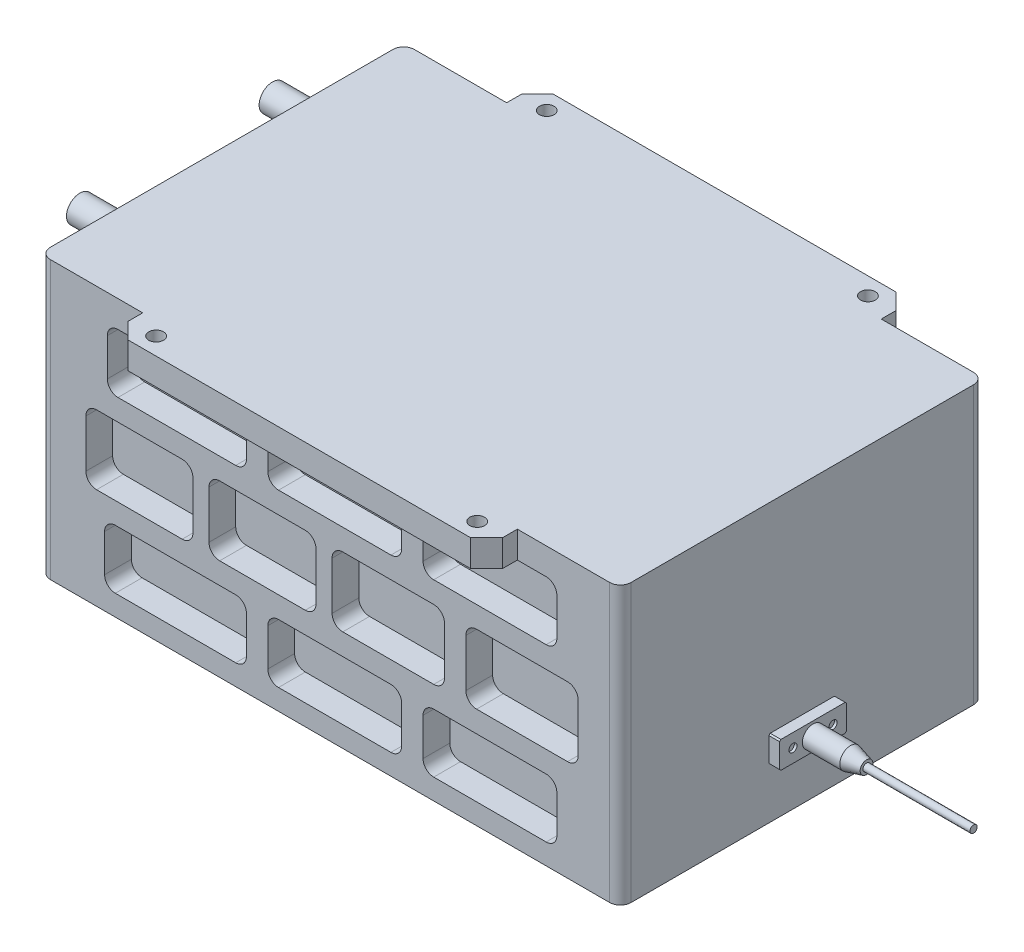
SolidWorks part; units mm, degrees
ref_plane "Front Plane" through (0, 0, 0) normal (0, 0, 1) x (1, 0, 0)
ref_plane "Top Plane" through (0, 0, 0) normal (0, 1, 0) x (1, 0, 0)
ref_plane "Right Plane" through (0, 0, 0) normal (1, 0, 0) x (0, 0, -1)
sketch "Sketch1" plane through (0, 0, 0) normal (0, 1, 0) x (1, 0, 0)
  line L1 (0, 0) -> (-217, 0)
  line L2 (0, 0) -> (0, 136)
  line L3 (0, 136) -> (-217, 136)
  line L4 (-217, 0) -> (-217, 136)
  dimension "D1" = 136
  dimension "D2" = 217
extrude "Boss-Extrude1" add sketch "Sketch1" along normal blind 103.6
sketch "Sketch2" plane through (0, 103.6, 0) normal (0, 1, 0) x (1, 0, 0)
  line L0 (-217, 0) -> (0, 0) construction
  line L1 (-178.5, 147.5) -> (-38.5, 147.5)
  line L2 (-178.5, 147.5) -> (-178.5, -11.5)
  line L3 (-178.5, -11.5) -> (-38.5, -11.5)
  line L4 (-38.5, 147.5) -> (-38.5, -11.5)
  line L5 (-217, 136) -> (-217, 0) construction
  dimension "D1" = 159
  dimension "D2" = 11.5
  dimension "D3" = 140
  dimension "D4" = 38.5
extrude "Boss-Extrude2" add sketch "Sketch2" against normal blind 10
sketch "Sketch3" plane through (0, 103.6, 0) normal (0, 1, 0) x (1, 0, 0)
  circle A0 centre (-168.5, 141) radius 2.75
  circle A1 centre (-48.5, 141) radius 2.75
  circle A2 centre (-168.5, -5) radius 2.75
  circle A3 centre (-48.5, -5) radius 2.75
  dimension "D5" = 5.5
  dimension "D6" = 5.5
  dimension "D7" = 5.5
  dimension "D8" = 5.5
  dimension "D1" = 120
  dimension "D3" = 146
extrude "Cut-Extrude1" cut sketch "Sketch3" against normal blind 10
sketch "Sketch5" plane through (0, 0, 0) normal (1, 0, 0) x (0, 0, -1)
  line L2 (55.5, 28.8) -> (80.5, 28.8)
  line L3 (55.5, 28.8) -> (55.5, 18.8)
  line L4 (55.5, 18.8) -> (80.5, 18.8)
  line L5 (80.5, 28.8) -> (80.5, 18.8)
  dimension "D3" = 25
  dimension "D5" = 10
extrude "Boss-Extrude3" add sketch "Sketch5" along normal blind 4
sketch "Sketch6" plane through (4, 0, 0) normal (1, 0, 0) x (0, 0, -1)
  line L1 (0, 103.6) -> (136, 103.6) construction
  circle A0 centre (68, 23.8) radius 4
  dimension "D1" = 8
  dimension "D2" = 79.8
extrude "Boss-Extrude4" add sketch "Sketch6" along normal blind 20
chamfer "Chamfer1" distance 6 angle 15 1 edges at (24, 23.8, -72)
sketch "Sketch7" plane through (-217, 0, 0) normal (-1, 0, 0) x (0, 0, 1)
  line L0 (-136, 103.6) -> (0, 103.6) construction
  circle A0 centre (-104, 93.6) radius 7.5
  circle A1 centre (-32, 93.6) radius 7.5
  point P6 (-68, 103.6)
  dimension "D1" = 72
  dimension "D2" = 36
  dimension "D3" = 15
  dimension "D4" = 15
  dimension "D5" = 10
extrude "Boss-Extrude5" add sketch "Sketch7" along normal blind 2
sketch "Sketch8" plane through (4, 0, 0) normal (1, 0, 0) x (0, 0, -1)
  circle A0 centre (75.5, 23.8) radius 1.5
  circle A1 centre (60.5, 23.8) radius 1.5
  circle A2 centre (68, 23.8) radius 2.3923 construction
  dimension "D1" = 15
  dimension "D2" = 7.5
  dimension "D3" = 3
  dimension "D4" = 3
extrude "Cut-Extrude2" cut sketch "Sketch8" against normal blind 1
chamfer "Chamfer2" distance 0.5 angle 45 4 edges at (2, 28.8, -55.5) (2, 28.8, -80.5) (2, 18.8, -55.5) (2, 18.8, -80.5)
chamfer "Chamfer3" distance 6 angle 45 4 edges at (-178.5, 98.6, -147.5) (-38.5, 98.6, -147.5) (-178.5, 98.6, 11.5) (-38.5, 98.6, 11.5)
sketch "Sketch9" plane through (-219, 0, 0) normal (-1, 0, 0) x (0, 0, 1)
  circle A0 centre (-104, 93.6) radius 5
  circle A1 centre (-32, 93.6) radius 5
  circle A2 centre (-104, 93.6) radius 4
  circle A3 centre (-32, 93.6) radius 4
  dimension "D1" = 10
  dimension "D2" = 10
  dimension "D3" = 8
  dimension "D4" = 8
extrude "Boss-Extrude6" add sketch "Sketch9" along normal blind 15
fillet "Fillet2" radius 4 4 edges at (-217, 51.8, 0) (-217, 51.8, -136) (0, 51.8, 0) (0, 51.8, -136)
sketch "Sketch11" plane through (0, 0, -136) normal (0, 0, -1) x (-1, 0, 0)
  line L0 (38.5, 93.6) -> (73.7445, 93.6)
  line L1 (178.5, 93.6) -> (191.7445, 93.6)
  line L2 (159.7445, 37.7329) -> (199.7445, 37.7329)
  line L4 (192.7445, 7.7329) -> (139.7445, 7.7329)
  line L5 (113.7445, 37.7329) -> (153.7445, 37.7329)
  line L7 (23.7445, 93.6) -> (38.5, 93.6)
  line L8 (23.7445, 71.6) -> (73.7445, 71.6)
  line L9 (15.7445, 63.6) -> (57.7445, 63.6)
  line L10 (15.7445, 37.7329) -> (57.7445, 37.7329)
  line L11 (23.7445, 29.7329) -> (73.7445, 29.7329)
  line L12 (23.7445, 93.6) -> (23.7445, 71.6)
  line L13 (73.7445, 93.6) -> (73.7445, 71.6)
  line L14 (81.7445, 93.6) -> (81.7445, 71.6)
  line L15 (131.7445, 93.6) -> (131.7445, 71.6)
  line L16 (139.7445, 93.6) -> (139.7445, 71.6)
  line L17 (191.7445, 93.6) -> (191.7445, 71.6)
  line L18 (57.7445, 63.6) -> (57.7445, 37.7329)
  line L19 (65.7445, 63.6) -> (65.7445, 37.7329)
  line L20 (81.7445, 71.6) -> (131.7445, 71.6)
  line L21 (81.7445, 93.6) -> (131.7445, 93.6)
  line L22 (139.7445, 93.6) -> (178.5, 93.6)
  line L23 (139.7445, 71.6) -> (191.7445, 71.6)
  line L24 (107.7445, 63.6) -> (107.7445, 37.7329)
  line L25 (113.7445, 63.6) -> (113.7445, 37.7329)
  line L26 (153.7445, 63.6) -> (153.7445, 37.7329)
  line L27 (159.7445, 63.6) -> (159.7445, 37.7329)
  line L28 (73.7445, 7.7329) -> (23.7445, 7.7329)
  line L29 (131.7445, 7.7329) -> (81.7445, 7.7329)
  line L30 (192.7445, 29.7329) -> (192.7445, 7.7329)
  line L31 (139.7445, 29.7329) -> (139.7445, 7.7329)
  line L32 (131.7445, 29.7329) -> (131.7445, 7.7329)
  line L33 (81.7445, 29.7329) -> (81.7445, 7.7329)
  line L34 (73.7445, 29.7329) -> (73.7445, 7.7329)
  line L35 (23.7445, 29.7329) -> (23.7445, 7.7329)
  line L36 (81.7445, 29.7329) -> (131.7445, 29.7329)
  line L37 (139.7445, 29.7329) -> (192.7445, 29.7329)
  line L38 (15.7445, 63.6) -> (15.7445, 37.7329)
  line L39 (199.7445, 63.6) -> (199.7445, 37.7329)
  line L40 (65.7445, 37.7329) -> (107.7445, 37.7329)
  line L41 (65.7445, 63.6) -> (107.7445, 63.6)
  line L42 (113.7445, 63.6) -> (153.7445, 63.6)
  line L43 (159.7445, 63.6) -> (199.7445, 63.6)
  dimension "D1" = 22
  dimension "D2" = 22
  dimension "D3" = 8
  dimension "D4" = 8
  dimension "D7" = 8
  dimension "D8" = 8
  dimension "D9" = 50
  dimension "D10" = 50
  dimension "D13" = 42
  dimension "D14" = 42
  dimension "D15" = 40
  dimension "D16" = 40
  dimension "D17" = 6
  dimension "D18" = 6
extrude "Cut-Extrude4" cut sketch "Sketch11" against normal blind 10
fillet "Fillet3" radius 4 40 edges at (-23.7445, 93.6, -131) (-81.7445, 93.6, -131) (-139.7445, 93.6, -131) (-159.7445, 63.6, -131) (-113.7445, 63.6, -131) (-15.7445, 63.6, -131) (-65.7445, 63.6, -131) (-23.7445, 29.7329, -131) (-81.7445, 29.7329, -131) (-139.7445, 29.7329, -131) (-23.7445, 71.6, -131) (-81.7445, 71.6, -131) (-139.7445, 71.6, -131) (-159.7445, 37.7329, -131) (-113.7445, 37.7329, -131) (-65.7445, 37.7329, -131) (-15.7445, 37.7329, -131) (-23.7445, 7.7329, -131) (-81.7445, 7.7329, -131) (-139.7445, 7.7329, -131) (-192.7445, 7.7329, -131) (-199.7445, 37.7329, -131) (-191.7445, 71.6, -131) (-131.7445, 71.6, -131) (-153.7445, 37.7329, -131) (-131.7445, 7.7329, -131) (-107.7445, 37.7329, -131) (-73.7445, 71.6, -131) (-57.7445, 37.7329, -131) (-73.7445, 7.7329, -131) (-57.7445, 63.6, -131) (-73.7445, 29.7329, -131) (-73.7445, 93.6, -131) (-131.7445, 93.6, -131) (-107.7445, 63.6, -131) (-131.7445, 29.7329, -131) (-153.7445, 63.6, -131) (-191.7445, 93.6, -131) (-199.7445, 63.6, -131) (-192.7445, 29.7329, -131)
ref_plane "Plane1" through (0, 0, -68) normal (0, 0, -1) x (-1, 0, 0)
mirror "Mirror1" about plane through (0, 0, -68) normal (0, 0, -1) of "Cut-Extrude4"
fillet "Fillet4" radius 4 40 edges at (-23.7445, 29.7329, -5) (-15.7445, 63.6, -5) (-23.7445, 93.6, -5) (-23.7445, 71.6, -5) (-81.7445, 93.6, -5) (-81.7445, 71.6, -5) (-65.7445, 63.6, -5) (-81.7445, 29.7329, -5) (-139.7445, 29.7329, -5) (-113.7445, 63.6, -5) (-159.7445, 63.6, -5) (-139.7445, 93.6, -5) (-139.7445, 71.6, -5) (-73.7445, 71.6, -5) (-73.7445, 93.6, -5) (-57.7445, 63.6, -5) (-107.7445, 63.6, -5) (-73.7445, 29.7329, -5) (-131.7445, 29.7329, -5) (-192.7445, 29.7329, -5) (-153.7445, 63.6, -5) (-131.7445, 71.6, -5) (-131.7445, 93.6, -5) (-191.7445, 71.6, -5) (-191.7445, 93.6, -5) (-199.7445, 63.6, -5) (-153.7445, 37.7329, -5) (-199.7445, 37.7329, -5) (-192.7445, 7.7329, -5) (-131.7445, 7.7329, -5) (-107.7445, 37.7329, -5) (-57.7445, 37.7329, -5) (-73.7445, 7.7329, -5) (-159.7445, 37.7329, -5) (-139.7445, 7.7329, -5) (-113.7445, 37.7329, -5) (-81.7445, 7.7329, -5) (-65.7445, 37.7329, -5) (-15.7445, 37.7329, -5) (-23.7445, 7.7329, -5)
sketch "Sketch13" plane through (24, 0, 0) normal (1, 0, 0) x (0, 0, -1)
  circle A0 centre (68, 23.8) radius 1.3477
extrude "Boss-Extrude7" add sketch "Sketch13" along normal blind 40
